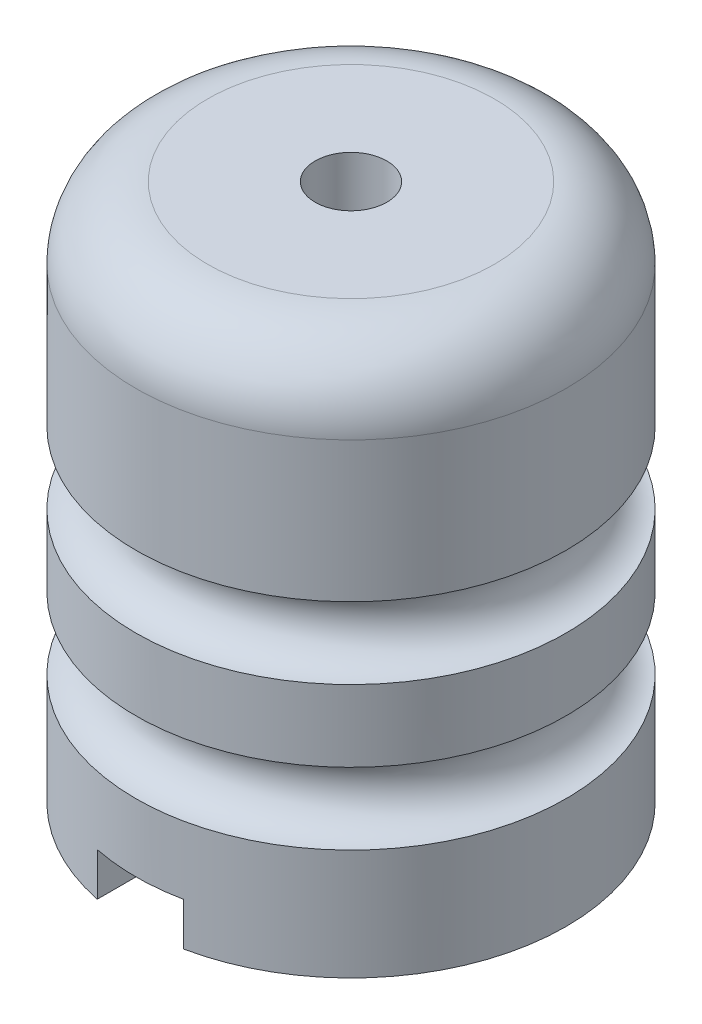
SolidWorks part; units mm, degrees
material "Brass"
ref_plane "Front Plane" through (0, 0, 0) normal (0, 0, 1) x (1, 0, 0)
ref_plane "Top Plane" through (0, 0, 0) normal (0, 1, 0) x (1, 0, 0)
ref_plane "Right Plane" through (0, 0, 0) normal (1, 0, 0) x (0, 0, -1)
sketch "Sketch1" plane through (0, 0, 0) normal (0, 0, 1) x (1, 0, 0)
  line L0 (0, 50.3) -> (0, -61.2204) construction
  line L1 (-97.9527, 0) -> (98.9454, 0) construction
  line L2 (0, -40.4504) -> (0, 34.5496)
  line L3 (30, 24.5496) -> (30, -40.4504)
  line L4 (30, -40.4504) -> (0, -40.4504)
  line L5 (0, 34.5496) -> (20, 34.5496)
  arc A0 (30, 24.5496) -> (20, 34.5496) centre (20, 24.5496) ccw
  dimension "D1" = 10
  dimension "D2" = 65
  dimension "D3" = 30
revolve "Revolve1" add sketch "Sketch1" angle 360 about L2
sketch "Sketch2" plane through (0, 0, 0) normal (0, 0, 1) x (1, 0, 0)
  line L0 (0, -46.3784) -> (0, 29.876) construction
  line L1 (-41.0011, 0) -> (46.1103, 0) construction
  line L2 (30, -40.4504) -> (30, 24.5496) construction
  circle A0 centre (30, 0) radius 5
  circle A1 centre (30, -20) radius 5
  dimension "D1" = 20
revolve "Cut-Revolve1" cut sketch "Sketch2" angle 360 about L0
sketch "Sketch3" plane through (0, 34.5496, 0) normal (0, 1, 0) x (1, 0, 0)
  circle A0 centre (0, 0) radius 5
extrude "Cut-Extrude1" cut sketch "Sketch3" against normal through all
sketch "Sketch4" plane through (0, -40.4504, 0) normal (0, -1, 0) x (1, 0, 0)
  circle A0 centre (0, 0) radius 22.2619
extrude "Cut-Extrude2" cut sketch "Sketch4" against normal blind 20
sketch "Sketch5" plane through (0, 0, 0) normal (0, 0, 1) x (1, 0, 0)
  line L0 (0, 20.6795) -> (0, -46.1229) construction
  line L1 (-30, -40.4504) -> (30, -40.4504) construction
  line L2 (-6, -34.4504) -> (6, -34.4504)
  line L3 (-6, -34.4504) -> (-6, -40.4504)
  line L4 (-6, -40.4504) -> (6, -40.4504)
  line L5 (6, -34.4504) -> (6, -40.4504)
  dimension "D1" = 12
  dimension "D2" = 6
  dimension "D3" = 6
extrude "Cut-Extrude3" cut sketch "Sketch5" against normal mid plane 70
